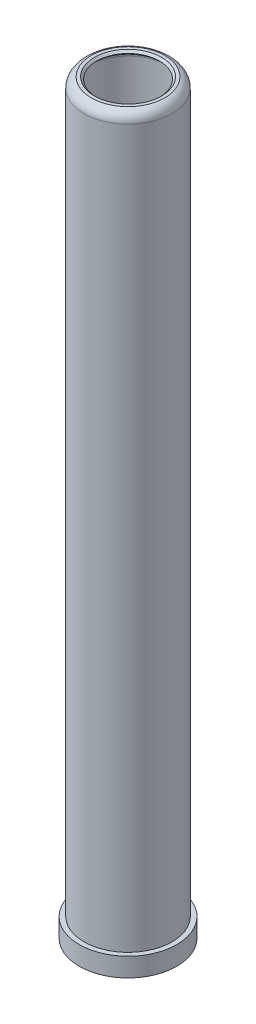
SolidWorks part; units mm, degrees
material "6061 Alloy"
ref_plane "Front Plane" through (0, 0, 0) normal (0, 0, 1) x (1, 0, 0)
ref_plane "Top Plane" through (0, 0, 0) normal (0, 1, 0) x (1, 0, 0)
ref_plane "Right Plane" through (0, 0, 0) normal (1, 0, 0) x (0, 0, -1)
sketch "Sketch1" plane through (0, 0, 0) normal (0, 0, 1) x (1, 0, 0)
  line L0 (0, -1085.2043) -> (0, 53175.0084) construction
  line L1 (12.5, 7) -> (12.5, 227.9669)
  line L2 (10.6731, 229.7938) -> (10, 230.4669)
  line L3 (10, 230.4669) -> (10.6731, 231.14)
  line L4 (10.6731, 231.14) -> (11.6731, 231.14)
  line L5 (14, 227.9669) -> (14, 0)
  line L6 (14, 0) -> (15.5, 0)
  line L7 (15.5, 0) -> (15.5, -6)
  line L8 (15.5, -6) -> (14.5, -6)
  line L9 (10, 2) -> (10, 7)
  line L10 (10, 7) -> (12.5, 7)
  line L11 (10, 2) -> (11, 2)
  line L12 (11, 2) -> (11, -1)
  line L13 (12.5, 0) -> (12.5, 7) construction
  arc A0 (12.5, 227.9669) -> (10.6731, 229.7938) centre (10.6731, 227.9669) ccw
  arc A1 (14, 227.9669) -> (11.6731, 231.14) centre (10.6731, 227.9669) ccw
  arc A2 (14.5, -6) -> (11, -1) centre (9.1786, -6) ccw
  dimension "D1" = 1.5
  dimension "D2" = 135
  dimension "D3" = 1
  dimension "D4" = 4
  dimension "D5" = 28
  dimension "D6" = 231.14
  dimension "D7" = 31
  dimension "D8" = 6
  dimension "D9" = 20
  dimension "D10" = 5
  dimension "D11" = 13
  dimension "D12" = 3
  dimension "D13" = 1
  dimension "D14" = 1
revolve "Revolve1" add sketch "Sketch1" angle 360 about L0
